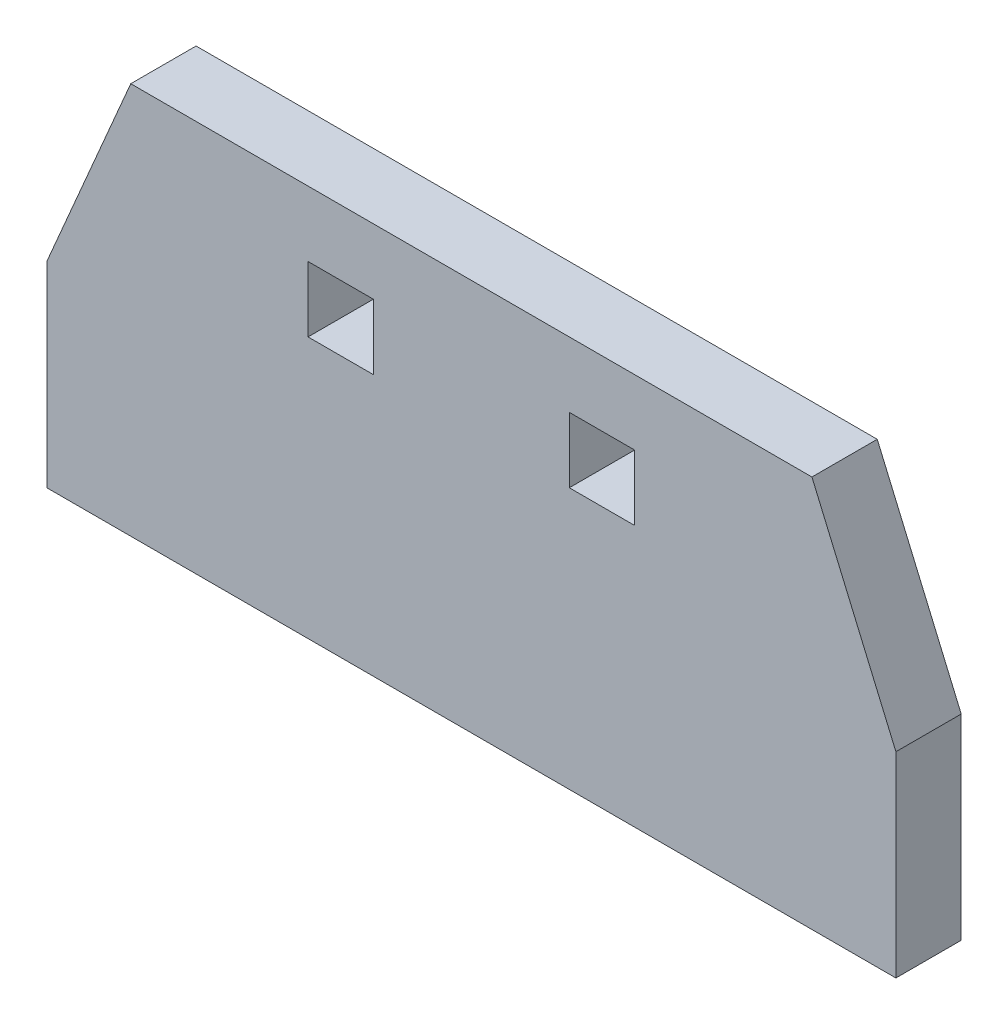
SolidWorks part; units mm, degrees
material "PLA"
ref_plane "Front Plane" through (0, 0, 0) normal (0, 0, 1) x (1, 0, 0)
ref_plane "Top Plane" through (0, 0, 0) normal (0, 1, 0) x (1, 0, 0)
ref_plane "Right Plane" through (0, 0, 0) normal (1, 0, 0) x (0, 0, -1)
sketch "Sketch1" plane through (0, 0, 0) normal (0, 0, 1) x (1, 0, 0)
  line L0 (-5, 75) -> (2.5, 25)
  line L1 (0, 0) -> (25, 0) construction
  line L2 (0, 0) -> (0, 75) construction
  line L3 (0, 75) -> (25, 75)
  line L4 (25, 0) -> (25, 75) construction
  line L5 (25, 75) -> (30, 75) construction
  line L6 (25, 75) -> (25, 100)
  line L7 (25, 100) -> (30, 100)
  line L8 (30, 75) -> (30, 100)
  line L9 (0, 75) -> (-5, 75) construction
  line L10 (0, 75) -> (0, 100)
  line L11 (0, 100) -> (-5, 100)
  line L12 (-5, 75) -> (-5, 100)
  line L13 (22.5, 0) -> (2.5, 0)
  line L14 (22.5, 0) -> (22.5, 25)
  line L15 (22.5, 25) -> (2.5, 25) construction
  line L16 (2.5, 0) -> (2.5, 25)
  line L17 (30, 75) -> (22.5, 25)
  point P15 (12.5, 25)
  point P16 (12.5, 75)
  dimension "D1" = 25
  dimension "D2" = 75
  dimension "D3" = 25
  dimension "D4" = 5
  dimension "D5" = 20
  dimension "D6" = 25
extrude "Boss-Extrude1" add sketch "Sketch1" along normal blind 2
sketch "Sketch2" plane through (0, 0, 0) normal (0, 0, -1) x (-1, 0, 0)
  line L0 (-30, 75) -> (-25, 75)
  line L1 (0, 75) -> (5, 75)
  line L2 (-22.5, 25) -> (-2.5, 25)
  line L12 (-25, 75) -> (-25, 100)
  line L13 (-25, 100) -> (-30, 100)
  line L14 (-30, 100) -> (-30, 75)
  line L15 (-30, 75) -> (-22.5, 25)
  line L16 (-22.5, 25) -> (-22.5, 0)
  line L17 (-22.5, 0) -> (-2.5, 0)
  line L18 (-2.5, 0) -> (-2.5, 25)
  line L19 (-2.5, 25) -> (5, 75)
  line L20 (5, 75) -> (5, 100)
  line L21 (5, 100) -> (0, 100)
  line L22 (0, 100) -> (0, 75)
  line L23 (0, 75) -> (-25, 75)
  line L24 (-25, 75) -> (-25, 100)
  line L25 (-25, 100) -> (-30, 100)
  line L26 (-30, 100) -> (-30, 75)
  line L28 (-22.5, 25) -> (-22.5, 0)
  line L29 (-22.5, 0) -> (-2.5, 0)
  line L30 (-2.5, 0) -> (-2.5, 25)
  line L32 (5, 75) -> (5, 100)
  line L33 (5, 100) -> (0, 100)
  line L34 (0, 100) -> (0, 75)
  dimension "D1" = 0
extrude "Boss-Extrude2" add sketch "Sketch2" along normal blind 20
sketch "Sketch3" plane through (0, 75, 0) normal (0, 1, 0) x (1, 0, 0)
  line L4 (25, 0) -> (0, 0)
  line L5 (0, 0) -> (0, -2)
  line L6 (0, -2) -> (25, -2)
  line L7 (25, -2) -> (25, 0)
  line L8 (25, 0) -> (0, 0)
  line L9 (0, 0) -> (0, -2)
  line L10 (0, -2) -> (25, -2)
  line L11 (25, -2) -> (25, 0)
  dimension "D1" = 0
extrude "Boss-Extrude3" add sketch "Sketch3" along normal up to surface (25 mm away) up to face at (27.5, 100, -9)
sketch "Sketch4" plane through (0, 0, 0) normal (0, 0, -1) x (-1, 0, 0)
  line L0 (-25, 75) -> (0, 75)
  line L8 (-2.5, 25) -> (5, 75)
  line L9 (5, 75) -> (0, 75)
  line L10 (0, 75) -> (0, 100)
  line L11 (0, 100) -> (-25, 100)
  line L12 (-25, 100) -> (-25, 75)
  line L13 (-25, 75) -> (-30, 75)
  line L14 (-30, 75) -> (-22.5, 25)
  line L15 (-22.5, 25) -> (-2.5, 25)
  line L18 (0, 75) -> (0, 100)
  line L19 (0, 100) -> (-25, 100)
  line L20 (-25, 100) -> (-25, 75)
  dimension "D1" = 0
extrude "Boss-Extrude4" add sketch "Sketch4" along normal blind 7
sketch "Sketch5" plane through (0, 0, 0) normal (0, 0, -1) x (-1, 0, 0)
  line L0 (5, 75) -> (5, 0)
  line L1 (5, 0) -> (-2.5, 0)
  line L2 (-22.5, 0) -> (-30, 0)
  line L3 (-30, 75) -> (-30, 0)
  line L8 (-30, 100) -> (-30, 75)
  line L9 (5, 100) -> (-30, 100)
  line L10 (5, 75) -> (5, 100)
  line L11 (-2.5, 25) -> (5, 75)
  line L12 (-2.5, 0) -> (-2.5, 25)
  line L13 (-22.5, 0) -> (-2.5, 0)
  line L14 (-22.5, 25) -> (-22.5, 0)
  line L15 (-30, 75) -> (-22.5, 25)
  line L16 (-30, 100) -> (-30, 75)
  line L17 (5, 100) -> (-30, 100)
  line L18 (5, 75) -> (5, 100)
  line L19 (-2.5, 25) -> (5, 75) construction
  line L20 (-2.5, 0) -> (-2.5, 25) construction
  line L21 (-22.5, 0) -> (-2.5, 0)
  line L22 (-22.5, 25) -> (-22.5, 0) construction
  line L23 (-30, 75) -> (-22.5, 25) construction
  dimension "D1" = 0
extrude "Boss-Extrude5" add sketch "Sketch5" against normal blind 5
sketch "Sketch6" plane through (0, 0, 5) normal (0, 0, 1) x (1, 0, 0)
  line L0 (30, 0) -> (-5, 0) construction
  line L1 (37.5, 0) -> (-12.5, 0)
  line L2 (2.5, 25) -> (22.5, 25) construction
  line L3 (-12.5, 25) -> (37.5, 25)
  line L4 (-12.5, 25) -> (-12.5, 0)
  line L5 (37.5, 25) -> (37.5, 0)
  point P4 (12.5, 25)
  point P6 (12.5, 25)
  dimension "D1" = 50
extrude "Boss-Extrude6" add sketch "Sketch6" against normal up to surface (5 mm away) up to face at (12.5, 25, 0)
sketch "Sketch8" plane through (0, 75, 0) normal (0, -1, 0) x (1, 0, 0)
  line L8 (-5, -20) -> (0, -20)
  line L9 (30, -20) -> (30, 0)
  line L10 (30, 0) -> (-5, 0)
  line L11 (-5, 0) -> (-5, -20)
  line L12 (-5, 0) -> (-5, -20)
  line L13 (-5, -20) -> (0, -20)
  line L14 (25, -20) -> (30, -20)
  line L15 (25, -7) -> (25, -20)
  line L16 (25, -20) -> (30, -20)
  line L17 (30, -20) -> (30, 0)
  line L18 (30, 0) -> (-5, 0)
  line L19 (0, -20) -> (0, -7)
  line L20 (0, -20) -> (0, -7)
  line L21 (0, -7) -> (25, -7)
  line L22 (0, -7) -> (25, -7)
  line L23 (25, -7) -> (25, -20)
  dimension "D1" = 0
extrude "Boss-Extrude7" add sketch "Sketch8" along normal blind 30
sketch "Sketch9" plane through (0, 100, 0) normal (0, 1, 0) x (1, 0, 0)
  line L8 (30, 20) -> (25, 20)
  line L9 (25, 20) -> (25, 7)
  line L10 (25, 7) -> (0, 7)
  line L11 (0, 7) -> (0, 20)
  line L12 (30, 20) -> (25, 20)
  line L13 (-5, 20) -> (-5, -5)
  line L14 (-5, -5) -> (30, -5)
  line L15 (30, -5) -> (30, 20)
  line L16 (0, 20) -> (-5, 20)
  line L17 (25, 20) -> (25, 7)
  line L18 (25, 7) -> (0, 7)
  line L19 (0, 7) -> (0, 20)
  line L20 (0, 20) -> (-5, 20)
  line L21 (-5, 20) -> (-5, -5)
  line L22 (-5, -5) -> (30, -5)
  line L23 (30, -5) -> (30, 20)
  dimension "D1" = 0
extrude "Cut-Extrude2" cut sketch "Sketch9" against normal blind 30
sketch "Sketch10" plane through (0, 0, -20) normal (0, 0, -1) x (-1, 0, 0)
  line L0 (-2.5, 25) -> (-22.5, 25) construction
  line L1 (-17.5, 25) -> (-7.5, 25) construction
  line L2 (-17.5, 25) -> (-17.5, 0)
  line L3 (-17.5, 0) -> (-7.5, 0) construction
  line L4 (-7.5, 25) -> (-7.5, 0)
  line L5 (-22.5, 0) -> (-2.5, 0) construction
  line L6 (-7.5, 0) -> (-2.5, 0)
  line L7 (-17.5, 25) -> (-22.5, 25)
  line L10 (-22.5, 25) -> (-22.5, 0)
  line L11 (-22.5, 0) -> (-2.5, 0)
  line L12 (-2.5, 0) -> (-2.5, 25)
  line L13 (-2.5, 25) -> (-22.5, 25)
  line L14 (-22.5, 25) -> (-22.5, 0)
  line L15 (-22.5, 0) -> (-17.5, 0)
  line L16 (-2.5, 0) -> (-2.5, 25)
  line L17 (-2.5, 25) -> (-7.5, 25)
  point P8 (-12.5, 25)
  point P9 (-12.5, 25)
  dimension "D1" = 10
  dimension "D2" = 0
extrude "Cut-Extrude3" cut sketch "Sketch10" against normal up to surface (20 mm away) up to face at (12.5, 20, 0)
sketch "Sketch11" plane through (0, 0, -7) normal (0, 0, -1) x (-1, 0, 0)
  line L4 (0, 45) -> (0, 70)
  line L5 (0, 70) -> (-25, 70)
  line L6 (-25, 70) -> (-25, 45)
  line L7 (-25, 45) -> (0, 45)
  line L8 (0, 45) -> (0, 70)
  line L9 (0, 70) -> (-25, 70)
  line L10 (-25, 70) -> (-25, 45)
  line L11 (-25, 45) -> (0, 45)
  dimension "D1" = 0
extrude "Cut-Extrude4" cut sketch "Sketch11" against normal up to surface (7 mm away) up to face at (12.5, 20, 0)
sketch "Sketch13" plane through (17.5, 0, 0) normal (1, 0, 0) x (0, 0, -1)
  line L0 (5, 25) -> (5, 20)
  line L1 (5, 20) -> (10, 20)
  line L2 (10, 20) -> (10, 5)
  line L3 (10, 5) -> (0, 5)
  line L4 (0, 25) -> (0, 0)
  line L5 (0, 0) -> (20, 0)
  line L6 (20, 0) -> (20, 25)
  line L7 (20, 25) -> (0, 25)
  line L8 (0, 25) -> (0, 5)
  line L9 (15, 0) -> (20, 0)
  line L10 (20, 0) -> (20, 25)
  line L11 (20, 25) -> (15, 25)
  line L12 (15, 25) -> (15, 0)
  line L13 (5, 25) -> (0, 25)
  dimension "D2" = 5
  dimension "D3" = 5
  dimension "D4" = 5
  dimension "D5" = 5
  dimension "D6" = 5
  dimension "D1" = 0
extrude "Cut-Extrude5" cut sketch "Sketch13" against normal up to surface (10 mm away) up to face at (7.5, 12.5, -10)
sketch "Sketch14" plane through (0, 0, -5) normal (0, 0, 1) x (1, 0, 0)
  line L4 (7.5, 25) -> (7.5, 20)
  line L5 (7.5, 20) -> (17.5, 20)
  line L6 (17.5, 20) -> (17.5, 25)
  line L7 (17.5, 25) -> (7.5, 25)
  line L8 (7.5, 25) -> (7.5, 20)
  line L9 (7.5, 20) -> (17.5, 20)
  line L10 (17.5, 20) -> (17.5, 25)
  line L11 (17.5, 25) -> (7.5, 25)
  dimension "D1" = 0
extrude "Boss-Extrude8" add sketch "Sketch14" along normal up to next
sketch "Sketch15" plane through (0, 0, -15) normal (0, 0, -1) x (-1, 0, 0)
  line L0 (-10, 0) -> (-10, 25)
  line L1 (-15, 25) -> (-15, 0)
  line L2 (-15, 25) -> (-17.5, 25)
  line L3 (-10, 0) -> (-7.5, 0)
  line L4 (-7.5, 0) -> (-7.5, 25)
  line L5 (-7.5, 25) -> (-17.5, 25)
  line L6 (-17.5, 25) -> (-17.5, 0)
  line L7 (-17.5, 0) -> (-7.5, 0)
  line L8 (-7.5, 0) -> (-7.5, 25)
  line L9 (-7.5, 25) -> (-10, 25)
  line L10 (-17.5, 25) -> (-17.5, 0)
  line L11 (-17.5, 0) -> (-15, 0)
  dimension "D1" = 0
  dimension "D2" = 2.5
extrude "Cut-Extrude6" cut sketch "Sketch15" against normal up to surface (15 mm away) up to face at (12.5, 26.875, 0)
sketch "Sketch16" plane through (0, 0, 5) normal (0, 0, 1) x (1, 0, 0)
  line L0 (-12.5, 25) -> (-12.5, 0) construction
  line L1 (-7.5, 20) -> (-2.5, 20)
  line L2 (-7.5, 20) -> (-7.5, 5)
  line L3 (-7.5, 5) -> (-2.5, 5)
  line L4 (-2.5, 20) -> (-2.5, 5)
  line L5 (-5, 25) -> (-12.5, 25) construction
  line L6 (37.5, 0) -> (-12.5, 0) construction
  line L7 (37.5, 0) -> (37.5, 25) construction
  line L8 (32.5, 20) -> (27.5, 20)
  line L9 (32.5, 20) -> (32.5, 5)
  line L10 (32.5, 5) -> (27.5, 5)
  line L11 (27.5, 20) -> (27.5, 5)
  point P8 (-8.75, 25)
  dimension "D1" = 5
  dimension "D2" = 5
  dimension "D3" = 5
  dimension "D4" = 5
  dimension "D5" = 5
extrude "Cut-Extrude7" cut sketch "Sketch16" against normal through all
sketch "Sketch17" plane through (30, 0, 0) normal (1, 0, 0) x (0, 0, -1)
  line L0 (20, 45) -> (0, 45) construction
  line L1 (0, 65) -> (5, 65)
  line L2 (0, 65) -> (0, 50)
  line L3 (0, 50) -> (5, 50)
  line L4 (5, 65) -> (5, 50)
  line L5 (0, 45) -> (0, 25) construction
  line L6 (-5, 70) -> (20, 70) construction
  dimension "D1" = 5
  dimension "D2" = 5
  dimension "D3" = 5
extrude "Cut-Extrude8" cut sketch "Sketch17" against normal through all
sketch "Sketch18" plane through (0, 0, 0) normal (0, 0, -1) x (-1, 0, 0)
  line L1 (0, 65) -> (-5, 65)
  line L2 (0, 65) -> (0, 50)
  line L3 (0, 50) -> (-5, 50)
  line L4 (-5, 65) -> (-5, 50)
  line L6 (-25, 50) -> (-20, 50)
  line L7 (-25, 50) -> (-25, 65)
  line L8 (-25, 65) -> (-20, 65)
  line L9 (-20, 50) -> (-20, 65)
  dimension "D1" = 5
extrude "Cut-Extrude9" cut sketch "Sketch18" against normal through all
sketch "Sketch19" plane through (30, 0, 0) normal (1, 0, 0) x (0, 0, -1)
  line L0 (5, 60) -> (10, 60)
  line L1 (5, 50) -> (5, 65) construction
  line L2 (10, 60) -> (10, 45)
  line L3 (20, 45) -> (0, 45) construction
  line L4 (10, 45) -> (20, 45)
  line L5 (20, 45) -> (20, 70)
  line L6 (20, 70) -> (-5, 70)
  line L7 (-5, 70) -> (-5, 60)
  line L9 (-5, 70) -> (-5, 25) construction
  line L10 (0, 60) -> (-5, 60)
  line L11 (0, 65) -> (0, 50) construction
  line L12 (0, 60) -> (5, 60)
  point P15 (7.5, 60)
  dimension "D1" = 15
  dimension "D2" = 5
extrude "Cut-Extrude10" cut sketch "Sketch19" against normal through all
sketch "Sketch20" plane through (30, 0, 0) normal (1, 0, 0) x (0, 0, -1)
  line L0 (10, 45) -> (15, 25)
  line L3 (0, 60) -> (0, 0)
  line L8 (10, 20) -> (10, 5)
  line L9 (10, 5) -> (0, 5)
  line L10 (0, 50) -> (0, 60)
  line L11 (0, 60) -> (-5, 60)
  line L12 (-5, 60) -> (-5, 25)
  line L13 (-5, 25) -> (0, 25)
  line L14 (0, 25) -> (0, 45)
  line L15 (0, 45) -> (10, 45)
  line L16 (10, 45) -> (10, 60)
  line L17 (10, 60) -> (5, 60)
  line L18 (5, 60) -> (5, 50)
  line L19 (5, 50) -> (0, 50)
  line L26 (10, 45) -> (10, 60)
  line L27 (10, 60) -> (0, 60)
  line L30 (0, 5) -> (0, 0)
  line L31 (0, 0) -> (15, 0)
  line L32 (15, 0) -> (15, 25)
  line L33 (15, 25) -> (0, 25)
  line L34 (0, 25) -> (0, 20)
  line L35 (0, 20) -> (10, 20)
  line L39 (0, 0) -> (15, 0)
  line L40 (15, 0) -> (15, 25)
  dimension "D1" = 0
  dimension "D2" = 0
extrude "Cut-Extrude11" cut sketch "Sketch20" against normal through all
sketch "Sketch21" plane through (0, 0, 0) normal (0, 0, -1) x (-1, 0, 0)
  line L0 (-5, 60) -> (-5, 50) construction
  line L1 (0, 60) -> (-5, 60)
  line L2 (0, 60) -> (0, 55)
  line L3 (0, 55) -> (-5, 55)
  line L4 (-5, 60) -> (-5, 55)
  line L5 (-25, 60) -> (-25, 50) construction
  line L6 (-20, 60) -> (-25, 60)
  line L7 (-20, 60) -> (-20, 55)
  line L8 (-20, 55) -> (-25, 55)
  line L9 (-25, 60) -> (-25, 55)
  line L11 (7.5, 20) -> (2.5, 20)
  line L12 (7.5, 20) -> (7.5, 5)
  line L13 (7.5, 5) -> (2.5, 5)
  line L14 (2.5, 20) -> (2.5, 5)
  line L15 (-27.5, 20) -> (-32.5, 20)
  line L16 (-27.5, 20) -> (-27.5, 5)
  line L17 (-27.5, 5) -> (-32.5, 5)
  line L18 (-32.5, 20) -> (-32.5, 5)
extrude "Boss-Extrude9" add sketch "Sketch21" against normal up to surface (5 mm away) up to face at (12.5, 41.25, 5)
sketch "Sketch22" plane through (0, 0, 0) normal (0, 0, -1) x (-1, 0, 0)
  line L0 (12.5, 25) -> (12.5, 0) construction
  line L1 (-10, 25) -> (-15, 25)
  line L2 (-10, 25) -> (-10, 20)
  line L3 (-10, 20) -> (-15, 20)
  line L4 (-15, 25) -> (-15, 20)
  line L5 (12.5, 15) -> (-37.5, 15)
  line L6 (12.5, 15) -> (12.5, 0)
  line L7 (12.5, 0) -> (-37.5, 0)
  line L8 (-37.5, 15) -> (-37.5, 0)
  line L9 (5, 25) -> (12.5, 25) construction
  point P13 (-12.5, 20)
  point P14 (-12.5, 15)
  dimension "D1" = 10
  dimension "D2" = 5
  dimension "D3" = 5
  dimension "D4" = 5
extrude "Cut-Extrude12" cut sketch "Sketch22" against normal through all
sketch "Sketch23" plane through (0, 0, 0) normal (0, 0, -1) x (-1, 0, 0)
  line L0 (0, 50) -> (0, 55) construction
  line L1 (-25, 35) -> (-20, 35)
  line L2 (-25, 35) -> (-25, 30)
  line L3 (-25, 30) -> (-20, 30)
  line L4 (-20, 35) -> (-20, 30)
  line L5 (-5, 35) -> (0, 35)
  line L6 (-5, 35) -> (-5, 30)
  line L7 (-5, 30) -> (0, 30)
  line L8 (0, 35) -> (0, 30)
  line L11 (-5, 50) -> (0, 50) construction
  line L12 (-25, 55) -> (-25, 50) construction
  point P10 (-22.5, 35)
  point P15 (-25, 32.5)
  point P16 (-20, 25.1499)
  dimension "D1" = 15
extrude "Cut-Extrude13" cut sketch "Sketch23" against normal through all
sketch "Sketch24" plane through (0, 25, 0) normal (0, -1, 0) x (1, 0, 0)
  line L1 (-12.5, 5) -> (-20, 5)
  line L3 (-12.5, 0) -> (-20, 0)
  line L4 (-12.5, 0) -> (37.5, 0)
  line L5 (37.5, 0) -> (37.5, 5)
  line L6 (37.5, 5) -> (-12.5, 5)
  line L7 (-12.5, 5) -> (-12.5, 0)
  line L8 (-12.5, 0) -> (37.5, 0)
  line L10 (37.5, 5) -> (-12.5, 5)
  line L12 (-20, 5) -> (-20, 0)
  line L13 (37.5, 5) -> (45, 5)
  line L15 (37.5, 0) -> (45, 0)
  line L16 (45, 5) -> (45, 0)
  dimension "D2" = 65
  dimension "D1" = 0
extrude "Boss-Extrude10" add sketch "Sketch24" along normal blind 15
sketch "Sketch25" plane through (0, 0, 5) normal (0, 0, 1) x (1, 0, 0)
  line L0 (45, 25) -> (30, 25) construction
  line L1 (30, 60) -> (30, 25) construction
  line L2 (-5, 25) -> (-5, 60) construction
  line L3 (-5, 25) -> (-20, 25) construction
  line L4 (45, 25) -> (30, 25)
  line L5 (30, 60) -> (30, 25)
  line L6 (-5, 25) -> (-5, 60)
  line L7 (-5, 25) -> (-20, 25)
  line L8 (30, 60) -> (45, 25)
  line L9 (-5, 60) -> (-20, 25)
extrude "Boss-Extrude11" add sketch "Sketch25" against normal through all
sketch "Sketch26" plane through (0, 60, 0) normal (0, 1, 0) x (1, 0, 0)
  line L4 (45, 0) -> (-20, 0)
  line L5 (45, -5) -> (45, 0)
  line L6 (-20, -5) -> (45, -5)
  line L7 (-20, 0) -> (-20, -5)
  line L8 (45, 0) -> (-20, 0)
  line L9 (45, -5) -> (45, 0)
  line L10 (-20, -5) -> (45, -5)
  line L11 (-20, 0) -> (-20, -5)
  dimension "D1" = 0
extrude "Cut-Extrude14" cut sketch "Sketch26" against normal offset from surface (20 mm away) 5 up to face at (22.5, 35, 2.5)
